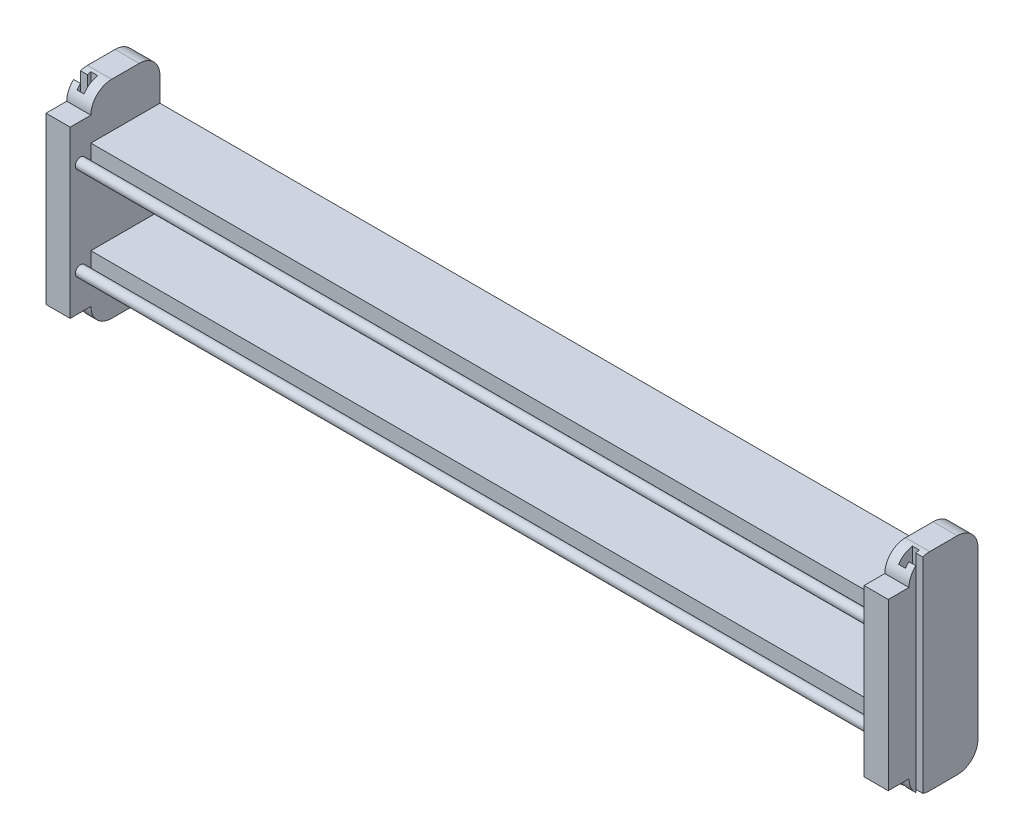
SolidWorks part; units mm, degrees
material "Plain Carbon Steel"
ref_plane "Front Plane" through (0, 0, 0) normal (0, 0, 1) x (1, 0, 0)
ref_plane "Top Plane" through (0, 0, 0) normal (0, 1, 0) x (1, 0, 0)
ref_plane "Right Plane" through (0, 0, 0) normal (1, 0, 0) x (0, 0, -1)
sketch "Sketch2" plane through (0, 0, 0) normal (0, 0, 1) x (1, 0, 0)
  line L1 (-1549.4, -381) -> (1549.4, -381)
  line L2 (-1549.4, -381) -> (-1549.4, 381)
  line L3 (-1549.4, 381) -> (1549.4, 381)
  line L4 (1549.4, -381) -> (1549.4, 381)
  line L5 (-1549.4, -381) -> (1549.4, 381) construction
  line L6 (-1549.4, 381) -> (1549.4, -381) construction
  point P0 (0, 0)
  dimension "D1" = 3098.8
  dimension "D2" = 762
extrude "Boss-Extrude1" add sketch "Sketch2" against normal blind 254
sketch "Sketch4" plane through (0, 0, 0) normal (0, 0, 1) x (1, 0, 0)
  line L1 (-1460.5, -127) -> (1460.5, -127)
  line L2 (-1460.5, -127) -> (-1460.5, 127)
  line L3 (-1460.5, 127) -> (1460.5, 127)
  line L4 (1460.5, -127) -> (1460.5, 127)
  line L5 (-1460.5, -127) -> (1460.5, 127) construction
  line L6 (-1460.5, 127) -> (1460.5, -127) construction
  point P0 (0, 0)
  dimension "D1" = 2921
  dimension "D2" = 254
extrude "Cut-Extrude2" cut sketch "Sketch4" against normal through all
sketch "Sketch5" plane through (0, 0, 0) normal (0, 0, 1) x (1, 0, 0)
  line L0 (1549.4, -381) -> (1549.4, 381) construction
  line L1 (-1460.5, 439.9683) -> (1460.5, 439.9683)
  line L2 (-1460.5, 439.9683) -> (-1460.5, 215.9)
  line L3 (-1460.5, 215.9) -> (1460.5, 215.9)
  line L4 (1460.5, 439.9683) -> (1460.5, 215.9)
  line L5 (-1460.5, 439.9683) -> (1460.5, 215.9) construction
  line L6 (-1460.5, 215.9) -> (1460.5, 439.9683) construction
  line L7 (-1460.5, -215.9) -> (1460.5, -215.9)
  line L8 (-1460.5, -215.9) -> (-1460.5, -425.3707)
  line L9 (-1460.5, -425.3707) -> (1460.5, -425.3707)
  line L10 (1460.5, -215.9) -> (1460.5, -425.3707)
  line L11 (-1460.5, -215.9) -> (1460.5, -425.3707) construction
  line L12 (-1460.5, -425.3707) -> (1460.5, -215.9) construction
  line L13 (-1549.4, -381) -> (-1549.4, 381) construction
  line L14 (-1460.5, 127) -> (1460.5, 127) construction
  line L15 (-1460.5, -127) -> (1460.5, -127) construction
  point P0 (0, 327.9342)
  point P5 (0, -320.6354)
  point P14 (1460.5, -320.6354)
  dimension "D1" = 88.9
  dimension "D2" = 88.9
  dimension "D3" = 88.9
  dimension "D4" = 88.9
  dimension "D5" = 88.9
  dimension "D6" = 88.9
extrude "Cut-Extrude3" cut sketch "Sketch5" against normal through all
sketch "Sketch7" plane through (0, -381, 0) normal (0, -1, 0) x (1, 0, 0)
  line L1 (1524, -12.6714) -> (1498.6, -12.6714)
  line L2 (1549.4, -25.3714) -> (1549.4, -50.7714)
  line L3 (1524, -63.4714) -> (1498.6, -63.4714)
  line L4 (1498.6, -12.6714) -> (1498.6, -63.4714)
  line L5 (1524, -12.6714) -> (1524, -25.3714)
  line L6 (1524, -25.3714) -> (1549.4, -25.3714)
  line L7 (1524, -50.7714) -> (1549.4, -50.7714)
  line L8 (1549.4, -25.3714) -> (1549.4, -50.7714)
  line L9 (1524, -50.7714) -> (1524, -63.4714)
  dimension "D3" = 12.7
  dimension "D4" = 12.7
extrude "Cut-Extrude5" cut sketch "Sketch7" against normal blind 762 and the other way through all contours L6 L5 L1 L4 L3 L9 L7
mirror "Mirror1" about plane through (0, 0, 0) normal (1, 0, 0) of "Cut-Extrude5"
fillet "Fillet1" radius 76.2 8 edges at (-1504.95, -381, 0) (-1504.95, -381, -254) (-1504.95, 381, 0) (-1504.95, 381, -254) (1504.95, 381, 0) (1504.95, 381, -254) (1504.95, -381, -254) (1504.95, -381, 0)
ref_plane "Plane1" through (1549.4, 0, 0) normal (1, 0, 0) x (0, 0, -1)
sketch "Sketch8" plane through (1549.4, 0, 0) normal (1, 0, 0) x (0, 0, -1)
  line L0 (0, -304.8) -> (0, 304.8) construction
  circle A0 centre (-38.1, 0) radius 38.1
  dimension "D1" = 76.2
sketch "Sketch9" plane through (0, 0, 0) normal (0, 0, 1) x (1, 0, 0)
  line L1 (1549.4, -304.8) -> (1460.5, -304.8)
  line L2 (1549.4, -304.8) -> (1549.4, 304.8)
  line L3 (1549.4, 304.8) -> (1460.5, 304.8)
  line L4 (1460.5, -304.8) -> (1460.5, 304.8)
  line L5 (1549.4, -304.8) -> (1460.5, 304.8) construction
  line L6 (1549.4, 304.8) -> (1460.5, -304.8) construction
  point P0 (1504.95, 0)
  dimension "D1" = 88.9
extrude "Boss-Extrude3" add sketch "Sketch9" along normal blind 76.2 contours L1 L4 L3 L2
mirror "Mirror6" about plane through (0, 0, 0) normal (1, 0, 0) of "Boss-Extrude3"
sketch "Sketch10" plane through (-1460.5, 0, 0) normal (1, 0, 0) x (0, 0, -1)
  line L1 (0, -215.9) -> (0, -127) construction
  circle A0 centre (-38.1, -171.45) radius 19.05
  dimension "D2" = 38.1
  dimension "D1" = 44.45
  dimension "D3" = 38.1
extrude "Boss-Extrude4" add sketch "Sketch10" along normal up to surface (2921 mm away) up to face at (1460.5, 0, -104.4222)
mirror "Mirror7" about plane through (0, 0, 0) normal (0, 1, 0) of "Boss-Extrude4"
